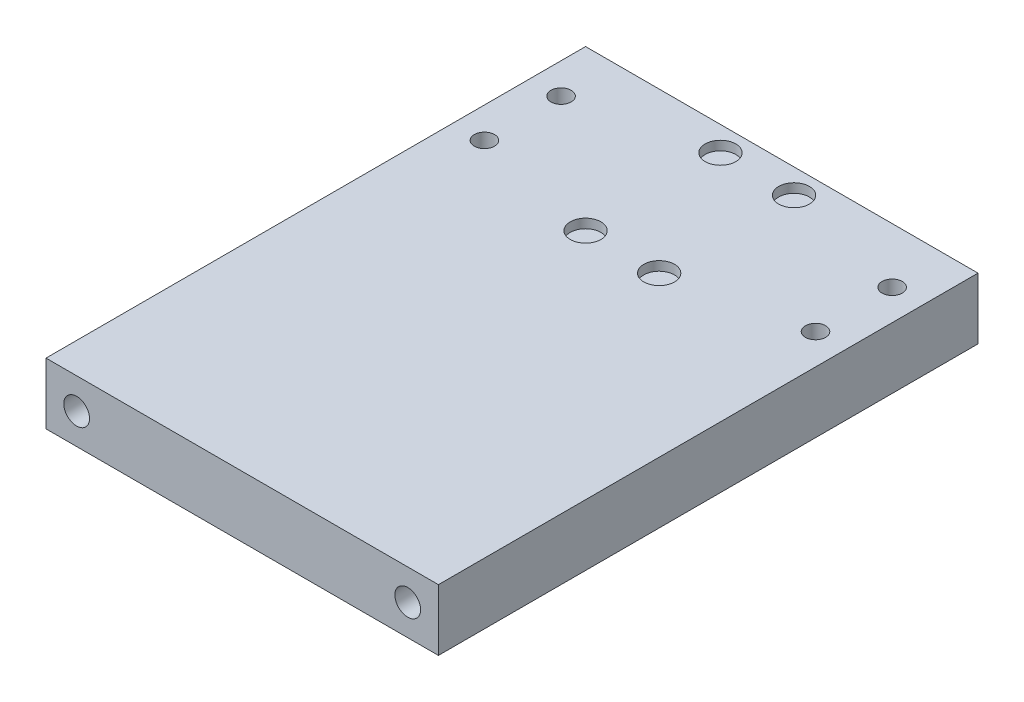
SolidWorks part; units mm, degrees
ref_plane "Front Plane" through (0, 0, 0) normal (0, 0, 1) x (1, 0, 0)
ref_plane "Top Plane" through (0, 0, 0) normal (0, 1, 0) x (1, 0, 0)
ref_plane "Right Plane" through (0, 0, 0) normal (1, 0, 0) x (0, 0, -1)
sketch "Sketch1" plane through (0, 0, 0) normal (1, 0, 0) x (0, 0, -1)
  line L0 (0, 60.5) -> (0, 0)
  line L1 (0, 0) -> (98, 0)
  line L2 (98, 0) -> (98, 10)
  line L3 (98, 10) -> (10, 10)
  line L4 (10, 10) -> (10, 60.5)
  line L5 (10, 60.5) -> (0, 60.5)
  dimension "D1" = 98
  dimension "D2" = 10
  dimension "D3" = 10
  dimension "D4" = 60.5
extrude "Boss-Extrude1" add sketch "Sketch1" along normal blind 64
ref_plane "Plane1" through (32, 0, 0) normal (-1, 0, 0) x (0, 0, 1)
sketch "Sketch3" plane through (0, 0, -10) normal (0, 0, -1) x (-1, 0, 0)
  line L0 (-64, 60.5) -> (0, 60.5) construction
  line L1 (-32, -4.4) -> (-32, 4.4) construction
  circle A0 centre (-47, 53.5) radius 2.25
  dimension "D1" = 7
  dimension "D3" = 4.5
  dimension "D2" = 15
extrude "Cut-Extrude1" cut sketch "Sketch3" against normal up to next (10 mm away)
pattern_linear "LPattern1" count 2 spacing 30 along (-1, 0, 0) count 2 spacing 20 along (0, -1, 0) of "Cut-Extrude1"
sketch "Sketch5" plane through (0, 0, -10) normal (0, 0, -1) x (-1, 0, 0)
  line L0 (-32, 55.3) -> (-32, 30.3) construction
  line L1 (-32, -4.4) -> (-32, 4.4) construction
  line L2 (-29.5, 55.3) -> (-29.5, 30.3)
  line L3 (-34.5, 55.3) -> (-34.5, 30.3)
  line L4 (-64, 60.5) -> (0, 60.5) construction
  arc A0 (-29.5, 55.3) -> (-34.5, 55.3) centre (-32, 55.3) ccw
  arc A1 (-34.5, 30.3) -> (-29.5, 30.3) centre (-32, 30.3) ccw
  point P4 (-32, 42.8)
  dimension "D2" = 2.5
  dimension "D3" = 25
  dimension "D1" = 5.2
extrude "Cut-Extrude3" cut sketch "Sketch5" against normal blind 10
sketch "Sketch6" plane through (0, 10, 0) normal (0, 1, 0) x (1, 0, 0)
  line L0 (64, 98) -> (0, 98) construction
  line L1 (64, 98) -> (64, 10) construction
  circle A0 centre (38, 94) radius 2.5
  dimension "D1" = 5
  dimension "D2" = 4
  dimension "D3" = 26
extrude "Cut-Extrude4" cut sketch "Sketch6" against normal blind 1.5
pattern_linear "LPattern3" count 2 spacing 12 along (-1, 0, 0) count 2 spacing 22 along (0, 0, 1) of "Cut-Extrude4"
chamfer "Chamfer1" [suppressed] distance 0.5 angle 45
sketch "Sketch7" plane through (64, 0, 0) normal (1, 0, 0) x (0, 0, -1)
  line L1 (10, 60.5) -> (103.832, 60.5)
  line L2 (10, 60.5) -> (10, -4.2572)
  line L3 (10, -4.2572) -> (103.832, -4.2572)
  line L4 (103.832, 60.5) -> (103.832, -4.2572)
extrude "Cut-Extrude5" [suppressed] cut sketch "Sketch7" against normal through all
sketch "Sketch8" plane through (0, 0, 0) normal (0, 0, 1) x (1, 0, 0)
  line L0 (64, 0) -> (0, 0) construction
  line L1 (64, 60.5) -> (64, 0) construction
  circle A0 centre (59, 5) radius 2.75
  dimension "D1" = 5.5
  dimension "D2" = 5
  dimension "D3" = 5
extrude "Cut-Extrude6" [suppressed] cut sketch "Sketch8" against normal through all
mirror "Mirror1" [suppressed] about plane through (32, 0, 0) normal (-1, 0, 0)
sketch "Sketch9" plane through (32, 0, 0) normal (-1, 0, 0) x (0, 0, 1)
  line L1 (-10, 60.5) -> (13.3252, 60.5)
  line L2 (-10, 60.5) -> (-10, -4.4514)
  line L3 (-10, -4.4514) -> (13.3252, -4.4514)
  line L4 (13.3252, 60.5) -> (13.3252, -4.4514)
extrude "Cut-Extrude7" cut sketch "Sketch9" against normal through all both and the other way through all
hole_wizard "M5 Tapped Hole1" positions "Sketch11" profile "Sketch10" tap size "M5" standard "ISO"
sketch "Sketch11" plane through (0, 0, -10) normal (0, 0, 1) x (1, 0, 0)
  line L0 (0, 10) -> (0, 0) construction
  line L1 (64, 0) -> (0, 0) construction
  line L2 (64, 10) -> (64, 0) construction
  point P0 (59, 5)
  point P2 (5, 5)
  dimension "D1" = 5
  dimension "D2" = 5
  dimension "D3" = 5
  dimension "D4" = 5
cosmetic thread "Hole Thread1" parameters "D1"=13, "D2"=5
cosmetic thread "Hole Thread2" parameters "D1"=13, "D2"=5
sketch "Sketch10" plane through (59, 5, -10) normal (1, 0, 0) x (0, -1, 0)
  line L0 (0, 0) -> (0, 19.2618)
  line L1 (0, 19.2618) -> (2.1, 18)
  line L2 (2.1, 18) -> (2.1, 0)
  line L5 (2.1, 0) -> (0, 0)
  line L10 (0, 19.2618) -> (-2.1, 18) construction
  line L11 (0, -6.35) -> (0, 107.95) construction
  dimension "Tap Drill Dia." = 4.2
  dimension "Tap Drill Depth" = 18
  dimension "Drill Angle" = 118
hole_wizard "M4 Tapped Hole1" positions "Sketch13" profile "Sketch12" tap size "M4" standard "ISO" end condition through all
sketch "Sketch13" plane through (0, 10, 0) normal (0, 1, 0) x (1, 0, 0)
  line L0 (64, 98) -> (64, 10) construction
  line L1 (0, 98) -> (0, 10) construction
  line L2 (64, 98) -> (0, 98) construction
  point P0 (59, 89)
  point P2 (59, 76.5)
  point P4 (5, 76.5)
  point P6 (5, 89)
  dimension "D1" = 5
  dimension "D2" = 5
  dimension "D3" = 12.5
  dimension "D4" = 9
  dimension "D5" = 9
  dimension "D6" = 12.5
sketch "Sketch12" plane through (59, 10, -89) normal (1, 0, 0) x (0, 0, 1)
  line L0 (0, 0) -> (0, 10)
  line L1 (0, 10) -> (1.65, 10)
  line L2 (1.65, 10) -> (1.65, 0)
  line L5 (1.65, 0) -> (0, 0)
  line L11 (0, -6.35) -> (0, 107.95) construction
  dimension "Thru Tap Drill Dia." = 3.3
  dimension "Thru Tap Drill Depth" = 10
cosmetic thread "Hole Thread3" parameters "D2"=4
cosmetic thread "Hole Thread4" parameters "D2"=4
cosmetic thread "Hole Thread5" parameters "D2"=4
cosmetic thread "Hole Thread6" parameters "D2"=4
